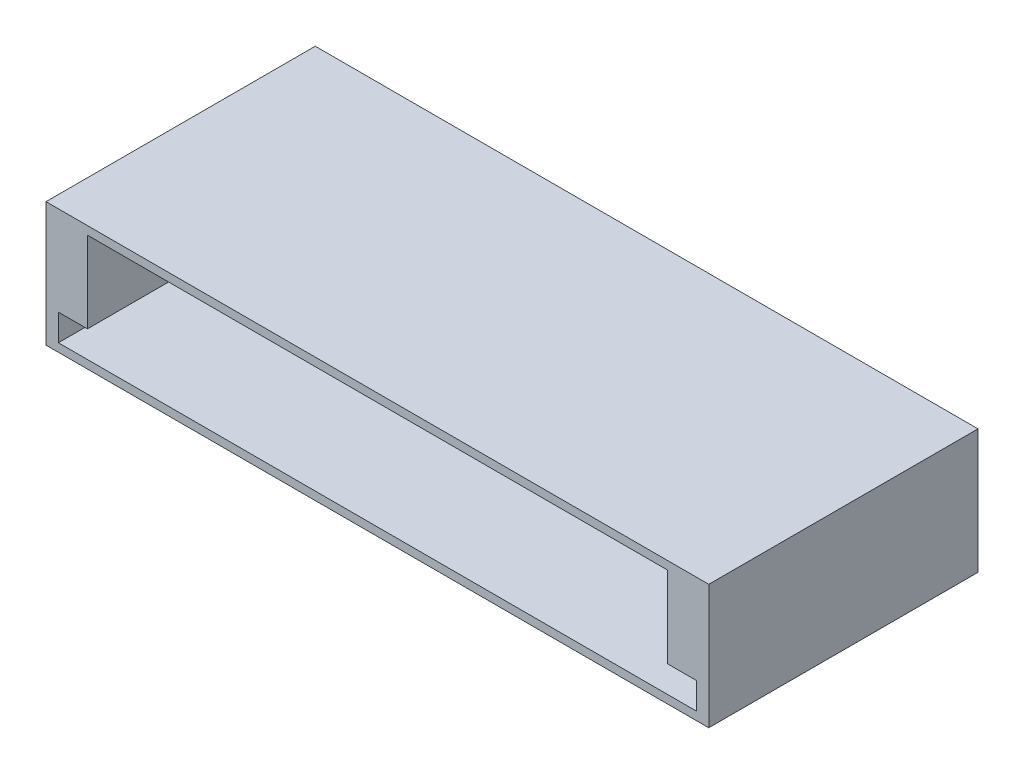
SolidWorks part; units mm, degrees
ref_plane "Front Plane" through (0, 0, 0) normal (0, 0, 1) x (1, 0, 0)
ref_plane "Top Plane" through (0, 0, 0) normal (0, 1, 0) x (1, 0, 0)
ref_plane "Right Plane" through (0, 0, 0) normal (1, 0, 0) x (0, 0, -1)
sketch "Çizim1" plane through (0, 0, 0) normal (0, 1, 0) x (1, 0, 0)
  line L1 (-54.8519, 9.6053) -> (25.1481, 9.6053)
  line L2 (-54.8519, 9.6053) -> (-54.8519, -22.8947)
  line L3 (-54.8519, -22.8947) -> (25.1481, -22.8947)
  line L4 (25.1481, 9.6053) -> (25.1481, -22.8947)
extrude "Yükseklik-Ekstrüzyon2" add sketch "Çizim1" along normal blind 15 contours L2 L1 L4 L3
sketch "Çizim2" plane through (0, 0, 22.8947) normal (0, 0, 1) x (1, 0, 0)
  line L0 (-54.8519, 15) -> (25.1481, 0) construction
  line L2 (-49.8519, 1) -> (20.1481, 1)
  line L3 (-49.8519, 1) -> (-49.8519, 14)
  line L4 (-49.8519, 14) -> (20.1481, 14)
  line L5 (20.1481, 1) -> (20.1481, 14)
  line L6 (-49.8519, 1) -> (20.1481, 14) construction
  line L7 (-49.8519, 14) -> (20.1481, 1) construction
  point P4 (-14.8519, 7.5)
extrude "Kes-Ekstrüzyon1" cut sketch "Çizim2" against normal blind 30
sketch "Çizim3" plane through (0, 0, 22.8947) normal (0, 0, 1) x (1, 0, 0)
  line L0 (-49.8519, 1) -> (-49.8519, 4.2) construction
  line L1 (-49.8519, 14) -> (-49.8519, 1) construction
  line L3 (-53.3519, 1) -> (23.6481, 1)
  line L4 (-49.8519, 1) -> (-53.3519, 1) construction
  line L5 (20.1481, 1) -> (23.6481, 1) construction
  line L6 (20.1481, 1) -> (20.1481, 4.2) construction
  line L7 (20.1481, 1) -> (20.1481, 14) construction
  line L8 (-53.3519, 1) -> (-53.3519, 4.2)
  line L9 (-53.3519, 4.2) -> (23.6481, 4.2)
  line L10 (23.6481, 1) -> (23.6481, 4.2)
extrude "Kes-Ekstrüzyon3" cut sketch "Çizim3" against normal blind 30
